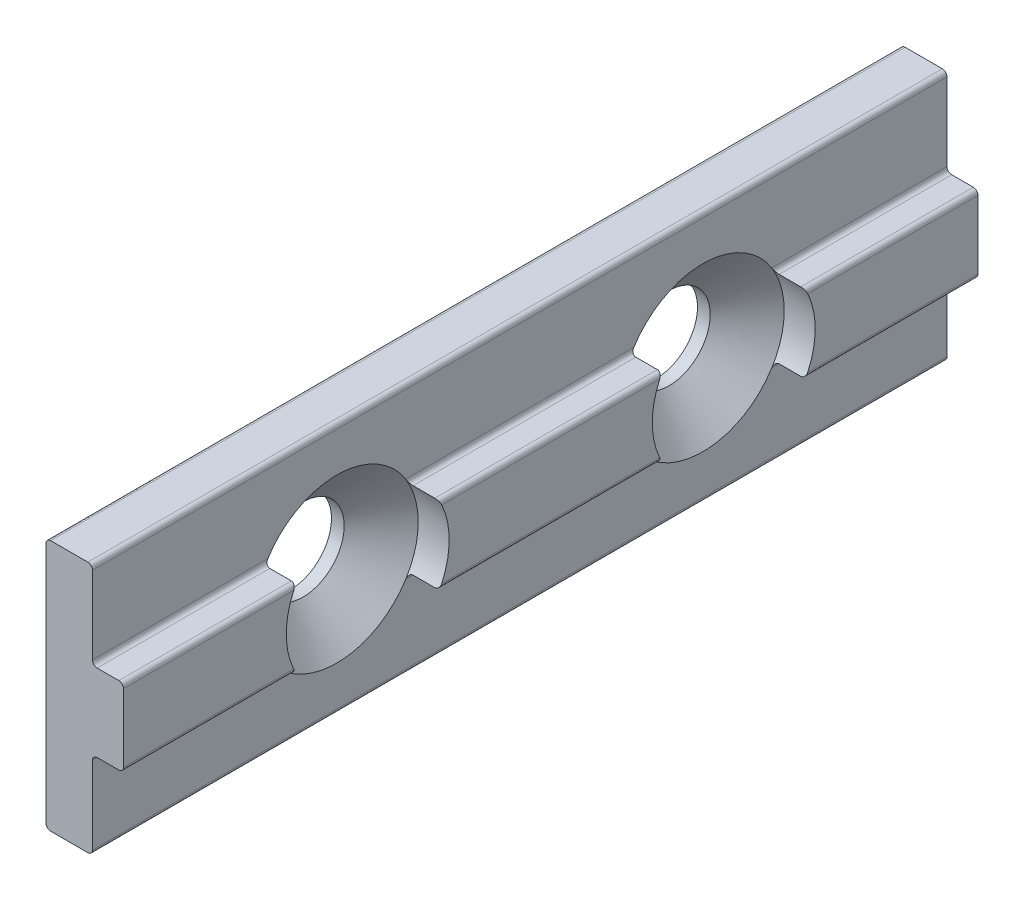
SolidWorks part; units mm, degrees
material "PTFE (general)"
ref_plane "Front Plane" through (0, 0, 0) normal (0, 0, 1) x (1, 0, 0)
ref_plane "Top Plane" through (0, 0, 0) normal (0, 1, 0) x (1, 0, 0)
ref_plane "Right Plane" through (0, 0, 0) normal (1, 0, 0) x (0, 0, -1)
ref_plane "Plane1" through (0, 0, 12.7) normal (0, 0, 1) x (1, 0, 0)
sketch "Sketch1" plane through (0, 0, 12.7) normal (0, 0, 1) x (1, 0, 0)
  line L0 (-3.81, 9.9314) -> (-3.81, -9.9314)
  line L1 (-3.429, -10.3124) -> (-0.381, -10.3124)
  line L2 (0, -9.9314) -> (0, -3.556)
  line L3 (0.381, -3.175) -> (2.159, -3.175)
  line L4 (2.54, -2.794) -> (2.54, 2.794)
  line L5 (2.159, 3.175) -> (0.381, 3.175)
  line L6 (0, 3.556) -> (0, 9.9314)
  line L7 (-0.381, 10.3124) -> (-3.429, 10.3124)
  arc A0 (-3.81, -9.9314) -> (-3.429, -10.3124) centre (-3.429, -9.9314) ccw
  arc A1 (-0.381, -10.3124) -> (0, -9.9314) centre (-0.381, -9.9314) ccw
  arc A2 (0, -3.556) -> (0.381, -3.175) centre (0.381, -3.556) cw
  arc A3 (2.159, -3.175) -> (2.54, -2.794) centre (2.159, -2.794) ccw
  arc A4 (2.54, 2.794) -> (2.159, 3.175) centre (2.159, 2.794) ccw
  arc A5 (0.381, 3.175) -> (0, 3.556) centre (0.381, 3.556) cw
  arc A6 (0, 9.9314) -> (-0.381, 10.3124) centre (-0.381, 9.9314) ccw
  arc A7 (-3.429, 10.3124) -> (-3.81, 9.9314) centre (-3.429, 9.9314) ccw
extrude "Boss-Extrude1" add sketch "Sketch1" against normal blind 70.04
sketch "Sketch2" plane through (2.54, 0, 0) normal (1, 0, 0) x (0, 0, -1)
  line L0 (-12.7, 0) -> (57.34, 0) construction
  line L1 (-12.7, -2.794) -> (-12.7, 2.794) construction
  line L2 (57.34, -2.794) -> (57.34, 2.794) construction
  line L3 (22.32, 2.794) -> (22.32, -2.794) construction
  line L4 (57.34, 2.794) -> (-12.7, 2.794) construction
  line L5 (57.34, -2.794) -> (-12.7, -2.794) construction
  line L6 (7.32, 2.794) -> (7.32, -2.794) construction
  line L7 (37.32, 2.794) -> (37.32, -2.794) construction
  point P12 (7.32, 0)
  point P13 (37.32, 0)
  dimension "D1" = 15
  dimension "D2" = 15
hole_wizard "CSK for 1/4 Flat Head Machine Screw (100)1" positions "Sketch6" profile "Sketch7" countersink size "1/4" standard "ANSI Inch" end condition up to next
sketch "Sketch6" plane through (0, 0, 0) normal (1, 0, 0) x (0, 0, -1)
  point P1 (37.32, 0)
  point P3 (7.32, 0)
sketch "Sketch7" plane through (0, 0, -37.32) normal (0, 1, 0) x (0, 0, -1)
  line L0 (0, 0) -> (0, 3.81)
  line L1 (0, 3.81) -> (3.3782, 3.81)
  line L2 (3.3782, 3.81) -> (3.3782, 2.7682)
  line L3 (3.3782, 2.7682) -> (6.6773, 0)
  line L5 (6.6773, 0) -> (0, 0)
  line L6 (-3.3782, 2.7682) -> (-6.6773, 0) construction
  line L11 (0, -6.35) -> (0, 107.95) construction
  dimension "Thru Hole Dia." = 6.7564
  dimension "Thru Hole Depth" = 3.81
  dimension "Near C'Sink Dia." = 13.3545
  dimension "Near C'Sink Angle" = 100
sketch "Sketch8" plane through (0, 0, 0) normal (1, 0, 0) x (0, 0, -1)
  arc A0 (31.6684, -3.556) -> (42.9716, -3.556) centre (37.32, 0) ccw construction
  arc A1 (42.9716, 3.556) -> (31.6684, 3.556) centre (37.32, 0) ccw construction
  arc A2 (1.6684, -3.556) -> (12.9716, -3.556) centre (7.32, 0) ccw construction
  arc A3 (12.9716, 3.556) -> (1.6684, 3.556) centre (7.32, 0) ccw construction
  arc A4 (31.6684, -3.556) -> (42.9716, -3.556) centre (37.32, 0) ccw construction
  arc A5 (42.9716, 3.556) -> (31.6684, 3.556) centre (37.32, 0) ccw construction
  arc A6 (1.6684, -3.556) -> (12.9716, -3.556) centre (7.32, 0) ccw construction
  arc A7 (12.9716, 3.556) -> (1.6684, 3.556) centre (7.32, 0) ccw construction
  circle A8 centre (7.32, 0) radius 6.6773
  circle A9 centre (37.32, 0) radius 6.6773
extrude "Cut-Extrude2" cut sketch "Sketch8" along normal up to next contours A8 | A9
